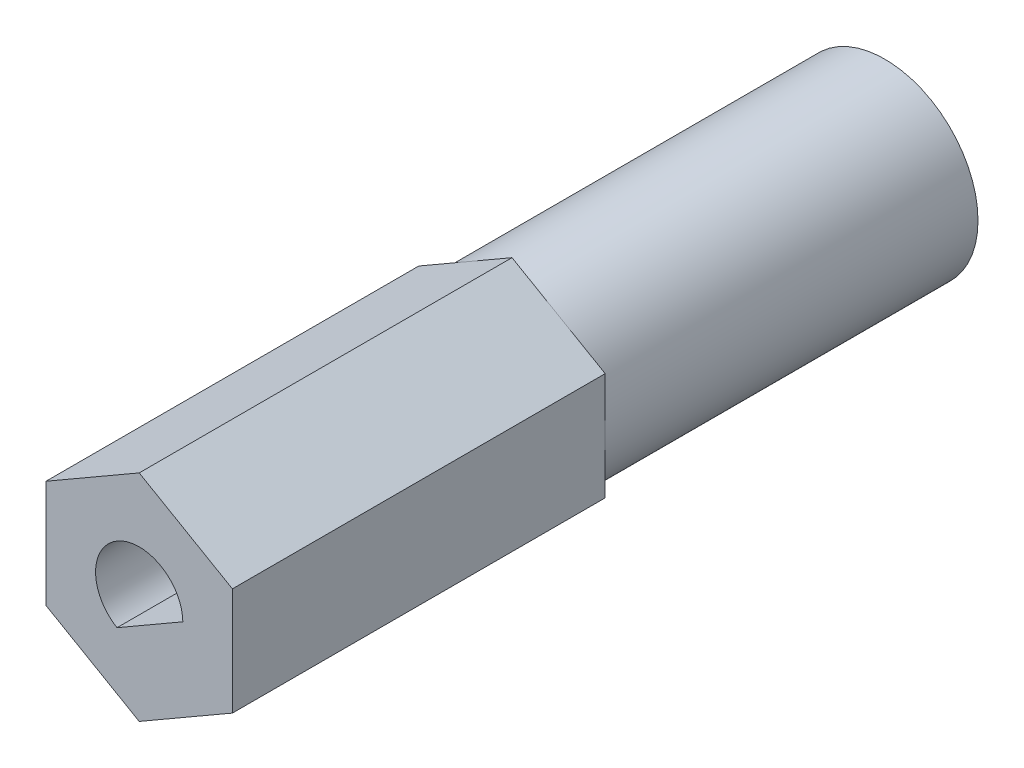
SolidWorks part; units mm, degrees
ref_plane "Front Plane" through (0, 0, 0) normal (0, 0, 1) x (1, 0, 0)
ref_plane "Top Plane" through (0, 0, 0) normal (0, 1, 0) x (1, 0, 0)
ref_plane "Right Plane" through (0, 0, 0) normal (1, 0, 0) x (0, 0, -1)
sketch "Sketch1" plane through (0, 0, 0) normal (0, 0, 1) x (1, 0, 0)
  line L1 (0, 3.6662) -> (-3.175, 1.8331)
  line L2 (-3.175, 1.8331) -> (-3.175, -1.8331)
  line L3 (-3.175, -1.8331) -> (0, -3.6662)
  line L4 (0, -3.6662) -> (3.175, -1.8331)
  line L5 (3.175, -1.8331) -> (3.175, 1.8331)
  line L6 (3.175, 1.8331) -> (0, 3.6662)
  circle A0 centre (0, 0) radius 3.175
  circle A1 centre (0, 0) radius 3.175 construction
  dimension "D1" = 6.35
extrude "Boss-Extrude1" add sketch "Sketch1" against normal blind 25.4 contours L1 L2 L3 L4 L5 L6
sketch "Sketch2" plane through (0, 0, 0) normal (0, 0, 1) x (1, 0, 0)
  line L0 (-0.7568, -1.2787) -> (1.4858, 0.0161)
  line L1 (0, 3.6662) -> (-3.175, 1.8331) construction
  arc A0 (1.4858, 0.0161) -> (-0.7568, -1.2787) centre (0, 0) ccw
  dimension "D1" = 1.4859
  dimension "D2" = 2.2149
extrude "Cut-Extrude1" cut sketch "Sketch2" against normal blind 5.08
ref_plane "Plane1" through (0, 0, -12.7) normal (0, 0, 1) x (1, 0, 0)
sketch "Sketch3" plane through (0, 0, -12.7) normal (0, 0, 1) x (1, 0, 0)
  circle A0 centre (0, 0) radius 3.175
  dimension "D1" = 6.35
extrude "Cut-Extrude2" cut sketch "Sketch3" against normal through all flip side to cut
